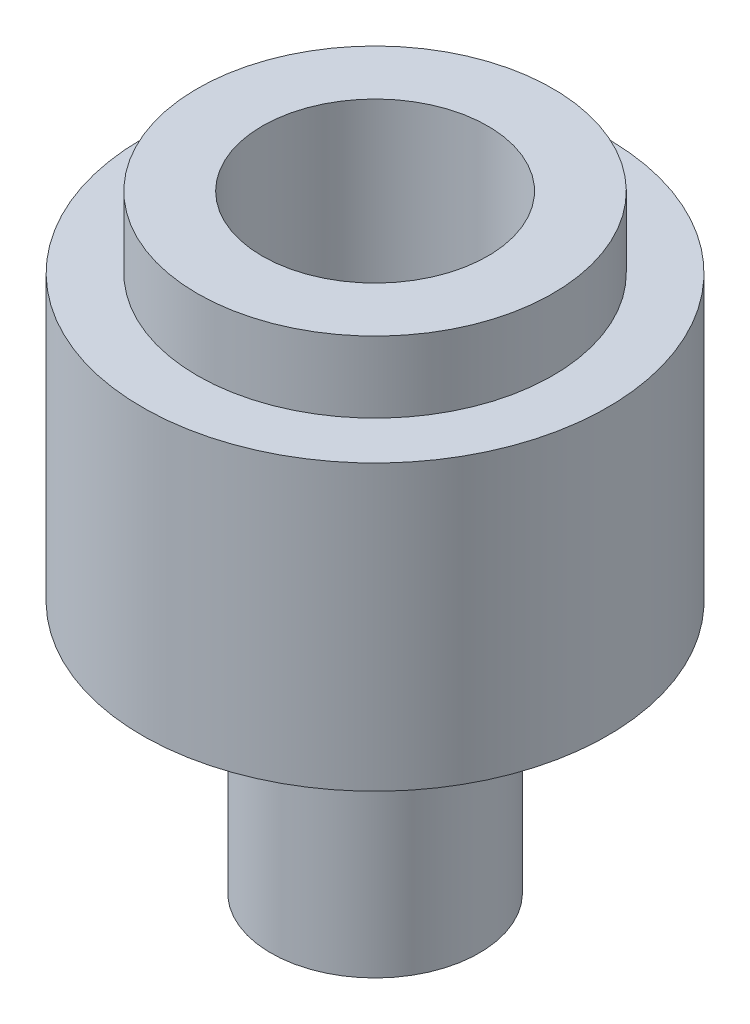
SolidWorks part; units mm, degrees
ref_plane "Front Plane" through (0, 0, 0) normal (0, 0, 1) x (1, 0, 0)
ref_plane "Top Plane" through (0, 0, 0) normal (0, 1, 0) x (1, 0, 0)
ref_plane "Right Plane" through (0, 0, 0) normal (1, 0, 0) x (0, 0, -1)
sketch "Sketch1" plane through (0, 0, 0) normal (0, 0, 1) x (1, 0, 0)
  line L0 (2.2, 1.2702) -> (0, 0)
  line L2 (2.2, 1.2702) -> (2.2, 5.0354)
  line L3 (2.2, 5.0354) -> (4.91, 6.6)
  line L4 (4.91, 6.6) -> (4.91, 12.6)
  line L5 (4.91, 12.6) -> (2.38, 12.6)
  line L6 (2.38, 12.6) -> (2.38, 8.0768)
  line L7 (2.38, 8.0768) -> (0, 6.6467)
  line L8 (0, 6.6467) -> (0, 0)
  point P1 (1.3673, 4.5132)
  point P9 (2.1056, 1.4671)
  point P10 (0, 4.8476)
  point P12 (0, 0)
  point P13 (-0.1063, 0)
  dimension "D1" = 60
  dimension "D2" = 2.2
  dimension "D3" = 4.91
  dimension "D4" = 6.6
  dimension "D5" = 6
  dimension "D6" = 59
  dimension "D7" = 2.38
revolve "Revolve1" add sketch "Sketch1" angle 360 about L8
sketch "Sketch3" plane through (0, 12.6, 0) normal (0, 1, 0) x (1, 0, 0)
  circle A0 centre (0, 0) radius 2.38
  circle A1 centre (0, 0) radius 3.75
  dimension "D1" = 4.76
  dimension "D2" = 7.5
extrude "Boss-Extrude1" add sketch "Sketch3" along normal blind 1.5
